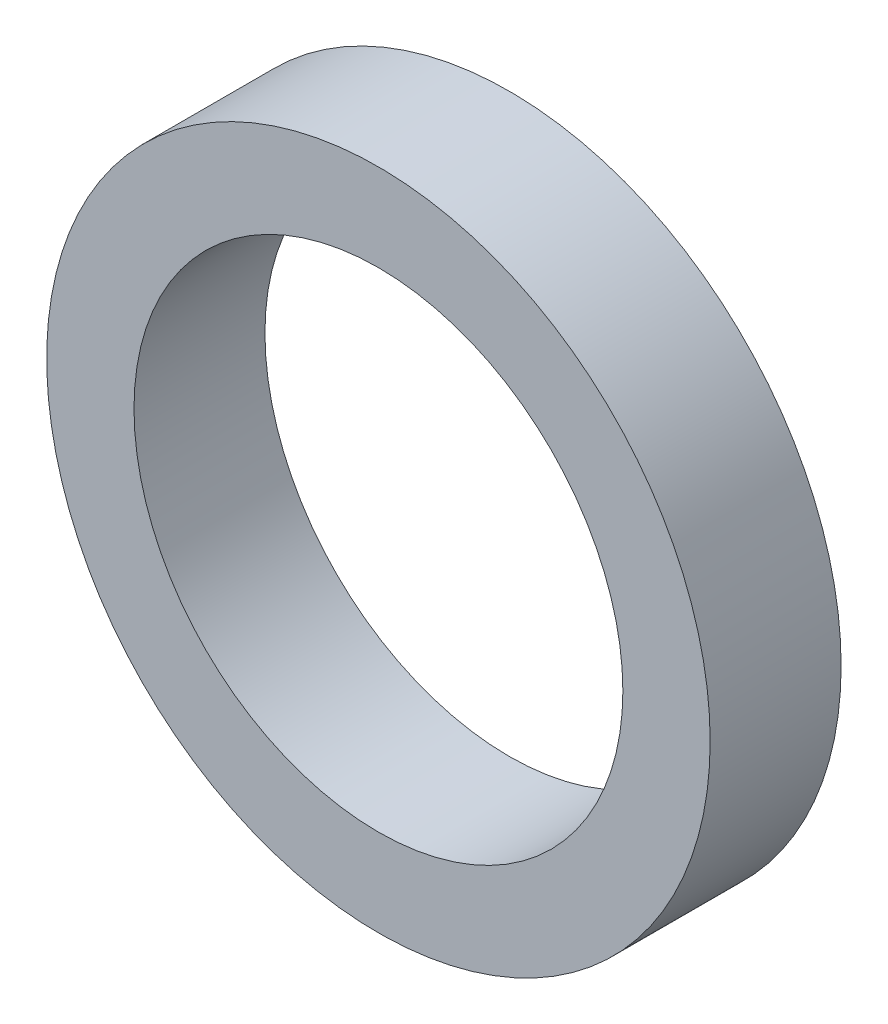
SolidWorks part; units mm, degrees
ref_plane "Front Plane" through (0, 0, 0) normal (0, 0, 1) x (1, 0, 0)
ref_plane "Top Plane" through (0, 0, 0) normal (0, 1, 0) x (1, 0, 0)
ref_plane "Right Plane" through (0, 0, 0) normal (1, 0, 0) x (0, 0, -1)
sketch "Sketch1" plane through (0, 0, 0) normal (0, 0, 1) x (1, 0, 0)
  circle A0 centre (0, 0) radius 4.826
  circle A1 centre (0, 0) radius 3.556
  dimension "D1" = 7.112
  dimension "D2" = 1.27
extrude "Boss-Extrude1" add sketch "Sketch1" along normal blind 1.905
